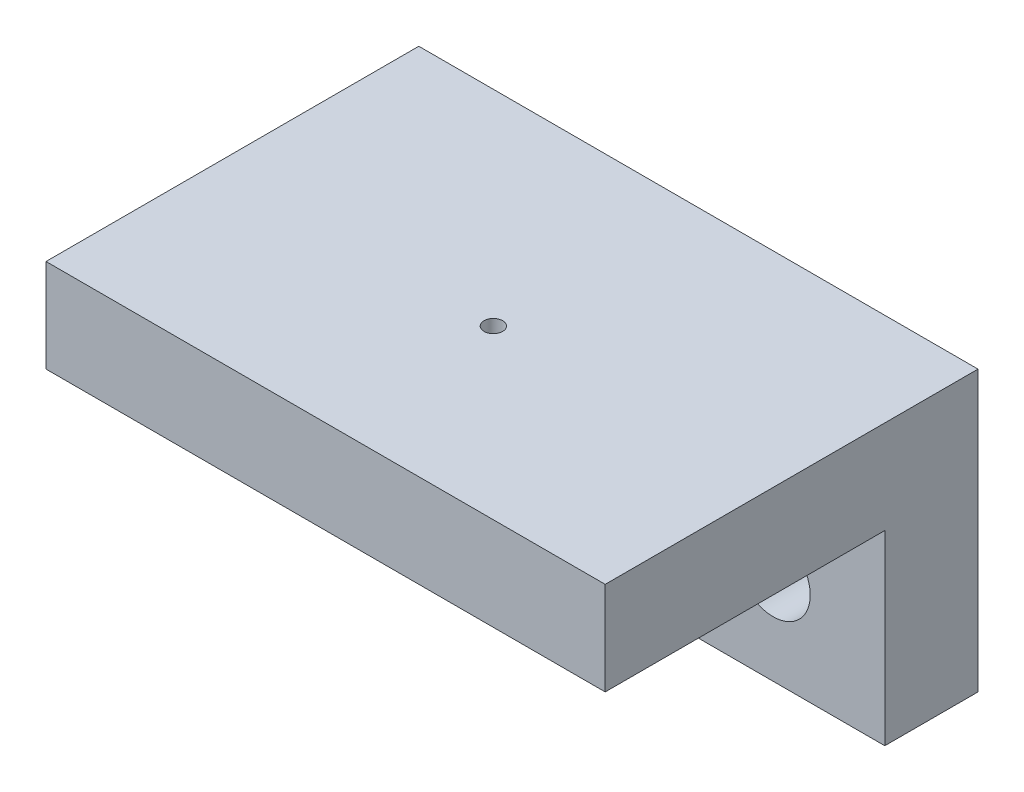
SolidWorks part; units mm, degrees
ref_plane "Alzado" through (0, 0, 0) normal (0, 0, 1) x (1, 0, 0)
ref_plane "Planta" through (0, 0, 0) normal (0, 1, 0) x (1, 0, 0)
ref_plane "Vista lateral" through (0, 0, 0) normal (1, 0, 0) x (0, 0, -1)
sketch "Croquis1" plane through (0, 0, 0) normal (0, 0, 1) x (1, 0, 0)
  line L1 (0, 0) -> (30, 0)
  line L2 (0, 0) -> (0, 15)
  line L3 (0, 15) -> (30, 15)
  line L4 (30, 0) -> (30, 15)
  dimension "D1" = 15
  dimension "D2" = 30
extrude "Saliente-Extruir1" add sketch "Croquis1" along normal blind 5
sketch "Croquis2" plane through (0, 0, 5) normal (0, 0, 1) x (1, 0, 0)
  line L0 (30, 0) -> (30, 15) construction
  line L1 (0, 15) -> (30, 15)
  line L2 (0, 15) -> (0, 10)
  line L3 (0, 10) -> (30, 10)
  line L4 (30, 15) -> (30, 10)
  dimension "D1" = 5
extrude "Saliente-Extruir2" add sketch "Croquis2" along normal blind 15
sketch "Croquis3" plane through (0, 0, 5) normal (0, 0, 1) x (1, 0, 0)
  line L0 (30, 5) -> (0, 5) construction
  line L1 (30, 0) -> (30, 10) construction
  line L2 (0, 10) -> (0, 0) construction
  circle A0 centre (24, 5) radius 2
  circle A1 centre (6, 5) radius 2
  dimension "D1" = 4
  dimension "D2" = 4
  dimension "D3" = 18
  dimension "D4" = 6
extrude "Cortar-Extruir1" cut sketch "Croquis3" against normal blind 15
sketch "Croquis4" plane through (0, 10, 0) normal (0, -1, 0) x (-1, 0, 0)
  line L0 (0, -20) -> (0, -5) construction
  line L1 (0, -5) -> (-30, -5) construction
  circle A0 centre (-15, -11) radius 0.5
  dimension "D1" = 1
  dimension "D2" = 15
  dimension "D3" = 6
extrude "Cortar-Extruir2" cut sketch "Croquis4" against normal blind 10
